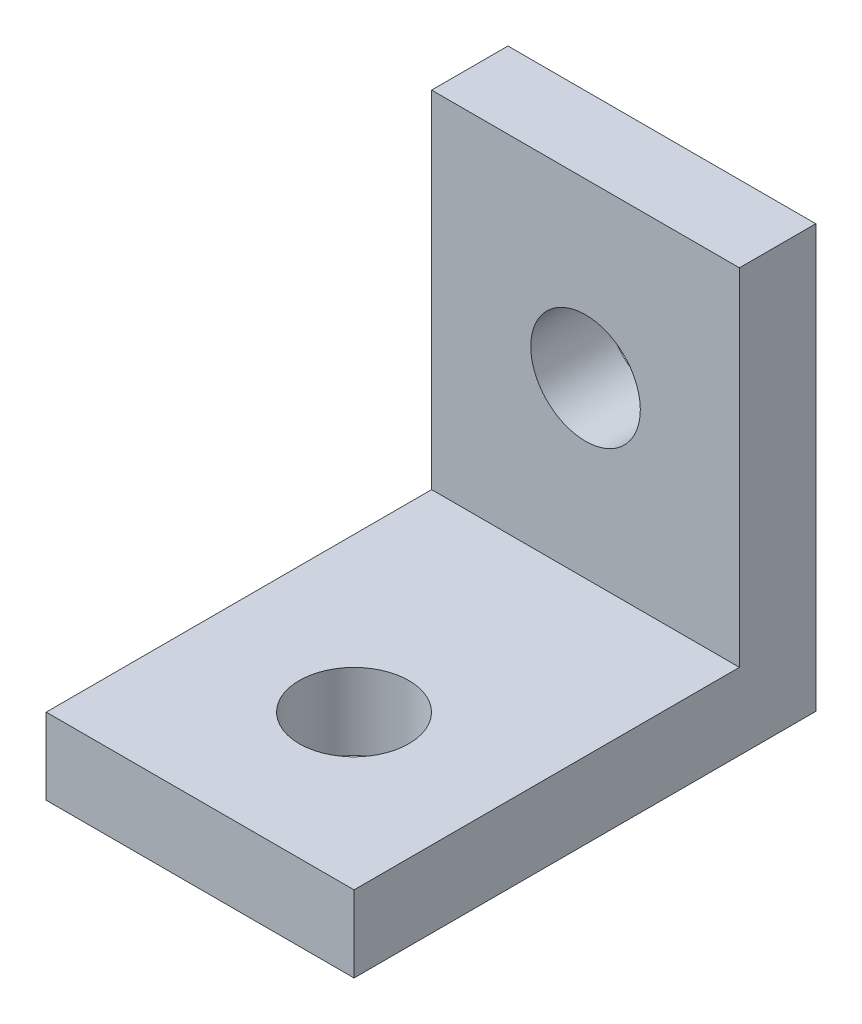
SolidWorks part; units mm, degrees
ref_plane "Front" through (0, 0, 0) normal (0, 0, 1) x (1, 0, 0)
ref_plane "Top" through (0, 0, 0) normal (0, 1, 0) x (1, 0, 0)
ref_plane "Right" through (0, 0, 0) normal (1, 0, 0) x (0, 0, -1)
sketch "Sketch1" plane through (0, 0, 0) normal (0, 1, 0) x (1, 0, 0)
  line L1 (3.175, -4.7625) -> (-3.175, -4.7625)
  line L2 (3.175, -4.7625) -> (3.175, 4.7625)
  line L3 (3.175, 4.7625) -> (-3.175, 4.7625)
  line L4 (-3.175, -4.7625) -> (-3.175, 4.7625)
  line L5 (3.175, -4.7625) -> (-3.175, 4.7625) construction
  line L6 (3.175, 4.7625) -> (-3.175, -4.7625) construction
  point P0 (0, 0)
  dimension "D1" = 9.525
  dimension "D2" = 6.35
extrude "Boss-Extrude1" add sketch "Sketch1" along normal blind 1.5748
sketch "Sketch2" plane through (0, 1.5748, 0) normal (0, 1, 0) x (1, 0, 0)
  line L0 (0, 4.7625) -> (0, -1.5875) construction
  line L1 (3.175, 4.7625) -> (-3.175, 4.7625) construction
  circle A0 centre (0, -1.5875) radius 1.1303
  dimension "D2" = 2.2606
  dimension "D1" = 6.35
extrude "Cut-Extrude1" cut sketch "Sketch2" against normal through all
sketch "Sketch3" plane through (0, 1.5748, 0) normal (0, 1, 0) x (1, 0, 0)
  line L0 (-3.175, 4.7625) -> (3.175, 4.7625)
  line L1 (-3.175, 4.7625) -> (-3.175, 3.1877)
  line L2 (3.175, 4.7625) -> (3.175, 3.1877)
  line L3 (-3.175, 3.1877) -> (3.175, 3.1877)
  dimension "D1" = 1.5748
extrude "Boss-Extrude2" add sketch "Sketch3" along normal blind 7.1374
sketch "Sketch4" plane through (0, 0, -3.1877) normal (0, 0, 1) x (1, 0, 0)
  line L0 (0, 0) -> (0, 5.1562) construction
  circle A0 centre (0, 5.1562) radius 1.1303
  dimension "D2" = 2.2606
  dimension "D1" = 5.1562
extrude "Cut-Extrude2" cut sketch "Sketch4" against normal through all
